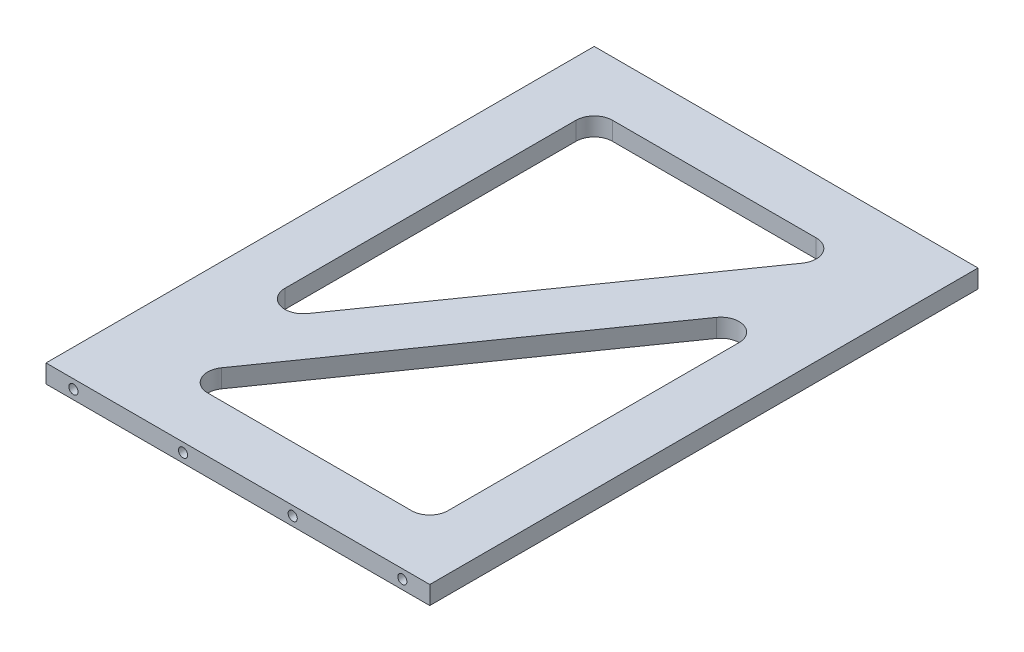
SolidWorks part; units mm, degrees
ref_plane "Front Plane" through (0, 0, 0) normal (0, 0, 1) x (1, 0, 0)
ref_plane "Top Plane" through (0, 0, 0) normal (0, 1, 0) x (1, 0, 0)
ref_plane "Right Plane" through (0, 0, 0) normal (1, 0, 0) x (0, 0, -1)
sketch "Sketch1" plane through (0, 0, 0) normal (0, 1, 0) x (1, 0, 0)
  line L1 (0, 0) -> (210, 0)
  line L2 (0, 0) -> (0, 300)
  line L3 (0, 300) -> (210, 300)
  line L4 (210, 0) -> (210, 300)
  dimension "D1" = 210
  dimension "D2" = 300
extrude "Boss-Extrude1" add sketch "Sketch1" along normal blind 10
sketch "Sketch2" plane through (0, 10, 0) normal (0, 1, 0) x (1, 0, 0)
  line L0 (39.3098, 30) -> (180, 30)
  line L1 (180, 30) -> (180, 230.986)
  line L2 (180, 230.986) -> (39.3098, 30)
  line L3 (0, 0) -> (210, 300) construction
  line L4 (0, 0) -> (210, 0) construction
  line L5 (210, 0) -> (210, 300) construction
  point P9 (105, 0)
  dimension "D1" = 30
  dimension "D2" = 30
  dimension "D3" = 15
extrude "Cut-Extrude1" cut sketch "Sketch2" against normal through all
sketch "Sketch3" plane through (0, 10, 0) normal (0, 1, 0) x (1, 0, 0)
  line L0 (30, 69.014) -> (30, 270)
  line L1 (30, 270) -> (170.6902, 270)
  line L2 (170.6902, 270) -> (30, 69.014)
  line L3 (0, 300) -> (0, 0) construction
  line L4 (210, 300) -> (0, 300) construction
  line L6 (0, 0) -> (210, 300) construction
  dimension "D1" = 30
  dimension "D2" = 30
  dimension "D3" = 15
extrude "Cut-Extrude2" cut sketch "Sketch3" against normal through all
fillet "Fillet1" radius 10 6 edges at (30, 5, -270) (180, 5, -230.986) (170.6902, 5, -270) (180, 5, -30) (30, 5, -69.014) (39.3098, 5, -30)
ref_plane "Plane1" through (0, 0, -150) normal (0, 0, -1) x (-1, 0, 0)
sketch "Sketch4" plane through (0, 0, 0) normal (0, 0, 1) x (1, 0, 0)
  line L0 (0, 10) -> (210, 10) construction
  line L1 (0, 10) -> (0, 0) construction
  line L2 (210, 10) -> (210, 0) construction
  circle A0 centre (15, 5) radius 2.5
  circle A1 centre (195, 5) radius 2.5
  circle A2 centre (135, 5) radius 2.5
  circle A3 centre (75, 5) radius 2.5
  dimension "D2" = 5
  dimension "D6" = 5
  dimension "D7" = 5
  dimension "D10" = 5
  dimension "D1" = 5
  dimension "D3" = 15
  dimension "D4" = 15
  dimension "D5" = 5
  dimension "D8" = 5
  dimension "D9" = 75
  dimension "D11" = 5
  dimension "D12" = 75
sketch "Sketch5" plane through (0, 0, -300) normal (0, 0, -1) x (-1, 0, 0)
  line L0 (0, 10) -> (0, 0) construction
  line L1 (-210, 10) -> (-210, 0) construction
  line L2 (-210, 10) -> (0, 10) construction
  circle A0 centre (-195, 5) radius 2.5
  circle A1 centre (-135, 5) radius 2.5
  circle A2 centre (-15, 5) radius 2.5
  circle A3 centre (-75, 5) radius 2.5
  point P10 (-210, 5)
  dimension "D1" = 5
  dimension "D2" = 5
  dimension "D3" = 5
  dimension "D8" = 5
  dimension "D6" = 5
  dimension "D4" = 15
  dimension "D5" = 15
  dimension "D7" = 5
  dimension "D9" = 5
  dimension "D10" = 5
  dimension "D11" = 75
  dimension "D12" = 75
hole_wizard "M6 Tapped Hole2" positions "Sketch12" profile "Sketch13" tap size "M6" standard "ISO"
sketch "Sketch12" plane through (0, 0, 0) normal (0, 0, 1) x (1, 0, 0)
  point P0 (15, 5)
  point P3 (135, 5)
  point P6 (195, 5)
  point P9 (75, 5)
sketch "Sketch13" plane through (15, 5, 0) normal (1, 0, 0) x (0, -1, 0)
  line L0 (0, 0) -> (0, 24.5022)
  line L1 (0, 24.5022) -> (2.5, 23)
  line L2 (2.5, 23) -> (2.5, 0)
  line L5 (2.5, 0) -> (0, 0)
  line L10 (0, 24.5022) -> (-2.5, 23) construction
  line L11 (0, -6.35) -> (0, 107.95) construction
  dimension "Tap Drill Dia." = 5
  dimension "Tap Drill Depth" = 23
  dimension "Drill Angle" = 118
cosmetic thread "Hole Thread1" parameters "D1"=17, "D2"=6
cosmetic thread "Hole Thread2" parameters "D1"=17, "D2"=6
cosmetic thread "Hole Thread3" parameters "D1"=17, "D2"=6
cosmetic thread "Hole Thread9" parameters "D1"=17, "D2"=6
hole_wizard "M6 Tapped Hole3" positions "Sketch14" profile "Sketch15" tap size "M6" standard "ISO"
sketch "Sketch14" plane through (0, 0, -300) normal (0, 0, -1) x (-1, 0, 0)
  point P0 (-195, 5)
  point P6 (-15, 5)
  point P10 (-135, 5)
  point P13 (-75, 5)
sketch "Sketch15" plane through (195, 5, -300) normal (1, 0, 0) x (0, 1, 0)
  line L0 (0, 0) -> (0, 21.5022)
  line L1 (0, 21.5022) -> (2.5, 20)
  line L2 (2.5, 20) -> (2.5, 0)
  line L5 (2.5, 0) -> (0, 0)
  line L10 (0, 21.5022) -> (-2.5, 20) construction
  line L11 (0, -6.35) -> (0, 107.95) construction
  dimension "Tap Drill Dia." = 5
  dimension "Tap Drill Depth" = 20
  dimension "Drill Angle" = 118
cosmetic thread "Hole Thread4" parameters "D1"=14, "D2"=6
cosmetic thread "Hole Thread6" parameters "D1"=14, "D2"=6
cosmetic thread "Hole Thread7" parameters "D1"=14, "D2"=6
cosmetic thread "Hole Thread8" parameters "D1"=14, "D2"=6
ref_plane "Plane2" through (105, 0, 0) normal (1, 0, 0) x (0, 0, -1)
